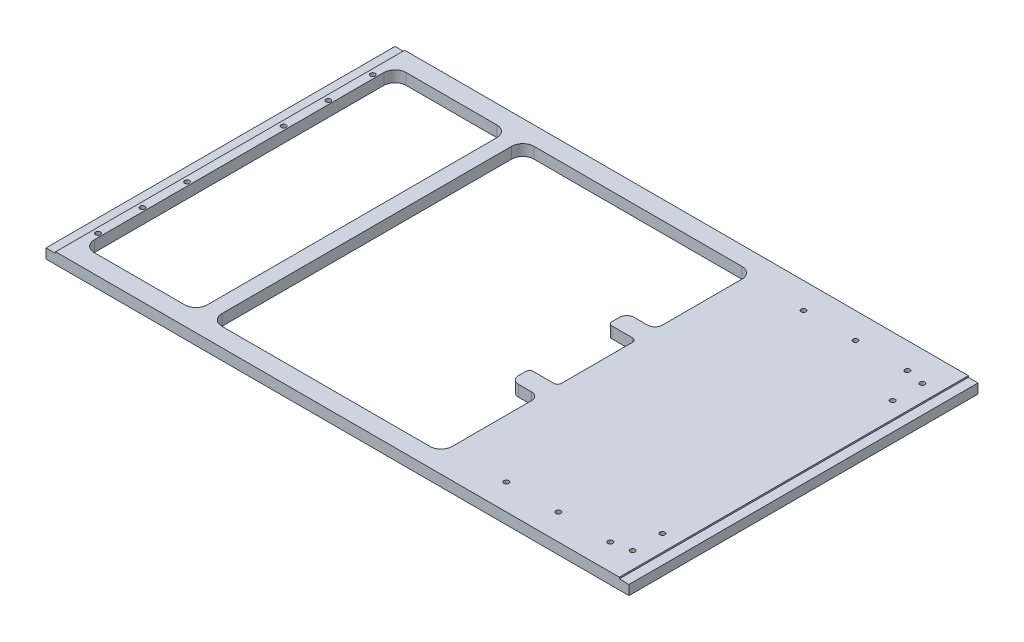
SolidWorks part; units mm, degrees
ref_plane "Front Plane" through (0, 0, 0) normal (0, 0, 1) x (1, 0, 0)
ref_plane "Top Plane" through (0, 0, 0) normal (0, 1, 0) x (1, 0, 0)
ref_plane "Right Plane" through (0, 0, 0) normal (1, 0, 0) x (0, 0, -1)
sketch "Sketch1" plane through (0, 0, 0) normal (0, 1, 0) x (1, 0, 0)
  line L1 (0, 0) -> (785, 0)
  line L2 (0, 0) -> (0, 470)
  line L3 (0, 470) -> (785, 470)
  line L4 (785, 0) -> (785, 470)
  dimension "D1" = 470
  dimension "D2" = 785
extrude "Boss-Extrude1" add sketch "Sketch1" along normal blind 15
sketch "Sketch2" plane through (0, 15, 0) normal (0, 1, 0) x (1, 0, 0)
  line L0 (785, 470) -> (0, 470) construction
  line L1 (25, 445) -> (177, 445)
  line L2 (25, 445) -> (25, 25)
  line L3 (25, 25) -> (177, 25)
  line L4 (177, 445) -> (177, 25)
  line L5 (0, 470) -> (0, 0) construction
  line L6 (0, 0) -> (785, 0) construction
  dimension "D1" = 25
  dimension "D2" = 25
  dimension "D3" = 25
  dimension "D4" = 152
extrude "Cut-Extrude1" cut sketch "Sketch2" against normal through all
sketch "Sketch3" plane through (0, 15, 0) normal (0, 1, 0) x (1, 0, 0)
  line L0 (177, 25) -> (177, 445) construction
  line L1 (197, 445) -> (507, 445)
  line L2 (197, 445) -> (197, 25)
  line L3 (197, 25) -> (507, 25)
  line L4 (507, 445) -> (507, 313)
  line L5 (177, 445) -> (25, 445) construction
  line L6 (25, 25) -> (177, 25) construction
  line L7 (507, 313) -> (469, 313)
  line L8 (469, 313) -> (469, 288)
  line L9 (469, 288) -> (507, 288)
  line L10 (507, 288) -> (507, 182)
  line L11 (507, 182) -> (469, 182)
  line L12 (469, 182) -> (469, 157)
  line L13 (469, 157) -> (507, 157)
  line L14 (507, 157) -> (507, 25)
  dimension "D1" = 20
  dimension "D2" = 310
  dimension "D3" = 132
  dimension "D4" = 25
  dimension "D5" = 38
  dimension "D6" = 25
  dimension "D7" = 132
  dimension "D8" = 38
extrude "Cut-Extrude2" cut sketch "Sketch3" against normal through all
fillet "Fillet1" radius 15 8 edges at (507, 7.5, -25) (197, 7.5, -25) (197, 7.5, -445) (507, 7.5, -445) (177, 7.5, -445) (177, 7.5, -25) (25, 7.5, -25) (25, 7.5, -445)
fillet "Fillet2" radius 10 4 edges at (507, 7.5, -157) (469, 7.5, -157) (469, 7.5, -313) (507, 7.5, -313)
fillet "Fillet3" radius 5 4 edges at (469, 7.5, -182) (507, 7.5, -182) (507, 7.5, -288) (469, 7.5, -288)
sketch "Sketch5" plane through (0, 0, 0) normal (0, 0, 1) x (1, 0, 0)
  line L1 (0, 15) -> (13, 15)
  line L2 (0, 15) -> (0, 13)
  line L3 (0, 13) -> (13, 13)
  line L4 (13, 15) -> (13, 13)
  dimension "D1" = 2
  dimension "D2" = 13
extrude "Cut-Extrude3" cut sketch "Sketch5" against normal through all
sketch "Sketch6" plane through (0, 0, 0) normal (0, 0, 1) x (1, 0, 0)
  line L1 (785, 15) -> (772, 15)
  line L2 (785, 15) -> (785, 13)
  line L3 (785, 13) -> (772, 13)
  line L4 (772, 15) -> (772, 13)
  dimension "D1" = 13
  dimension "D2" = 2
extrude "Cut-Extrude4" cut sketch "Sketch6" against normal through all
ref_plane "Plane1" through (0, 0, -235) normal (0, 0, -1) x (-1, 0, 0)
ref_plane "Plane2" through (392.5, 0, 0) normal (-1, 0, 0) x (0, 0, 1)
hole_wizard "Ø6.6 (6.6) Diameter Slot1" positions "Sketch9" profile "Sketch8" size "Ø6.6" standard "ISO" slot yes end condition through all
sketch "Sketch9" plane through (0, 0, 0) normal (0, -1, 0) x (-1, 0, 0)
  point P0 (-20, 50)
  point P3 (-20, 110)
  point P6 (-20, 170)
  point P9 (-20, 300)
  point P12 (-20, 360)
  point P15 (-20, 420)
  point P19 (-585, 435)
  point P22 (-655, 435)
  point P30 (-725, 435)
  point P33 (-750, 430)
  point P36 (-750, 390)
  point P39 (-750, 80)
  point P42 (-750, 40)
  point P45 (-725, 35)
  point P51 (-655, 35)
  point P54 (-585, 35)
sketch "Sketch8" plane through (20, 0, -50) normal (1, 0, 0) x (0, 0, -1)
  line L0 (0, 0) -> (0, 15)
  line L1 (0, 15) -> (3.3, 15)
  line L2 (3.3, 15) -> (3.3, 0)
  line L5 (3.3, 0) -> (0, 0)
  line L11 (0, -6.35) -> (0, 107.95) construction
  dimension "Thru Hole Dia." = 6.6
  dimension "Thru Hole Depth" = 15
